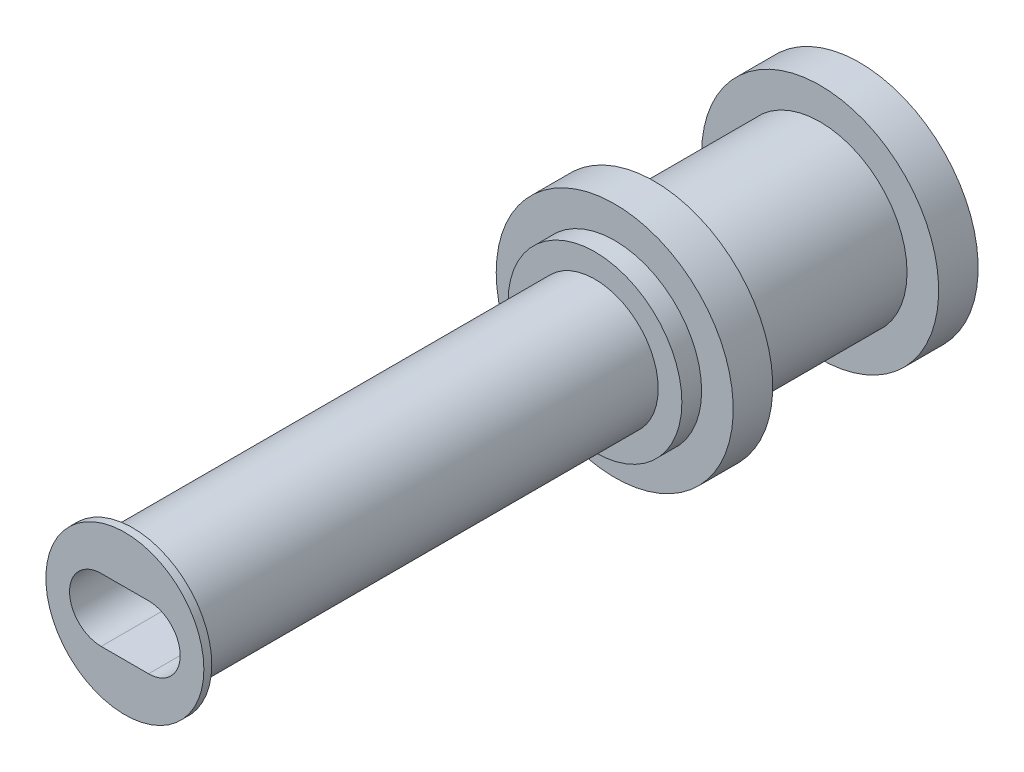
SolidWorks part; units mm, degrees
material "PVC Rigid"
ref_plane "Front Plane" through (0, 0, 0) normal (0, 0, 1) x (1, 0, 0)
ref_plane "Top Plane" through (0, 0, 0) normal (0, 1, 0) x (1, 0, 0)
ref_plane "Right Plane" through (0, 0, 0) normal (1, 0, 0) x (0, 0, -1)
sketch "Sketch1" plane through (0, 0, 0) normal (0, 0, 1) x (1, 0, 0)
  line L0 (-7.874, 0) -> (7.874, 0) construction
  line L1 (6.35, 0) -> (9.398, 0) construction
  line L2 (6.35, 0.762) -> (9.398, 0.762)
  line L10 (6.35, -0.762) -> (9.398, -0.762)
  line L19 (7.874, 1.524) -> (7.874, -1.524) construction
  line L20 (8.636, 1.524) -> (8.636, -1.524)
  line L21 (7.112, 1.524) -> (7.112, -1.524)
  line L22 (6.35, 0) -> (9.398, 0) construction
  circle A0 centre (7.874, 0) radius 2.794
  arc A2 (6.35, 0.762) -> (6.35, -0.762) centre (6.35, 0) ccw
  circle A4 centre (7.874, 0) radius 2.54
  arc A5 (9.398, -0.762) -> (9.398, 0.762) centre (9.398, 0) ccw
  circle A23 centre (7.874, 0) radius 2.286 construction
  arc A24 (8.636, 1.524) -> (7.112, 1.524) centre (7.874, 1.524) ccw
  arc A25 (7.112, -1.524) -> (8.636, -1.524) centre (7.874, -1.524) ccw
  point P13 (9.525, 0)
  point P14 (7.874, 0)
  point P15 (7.62, 0)
  point P17 (0, 3.302)
  point P18 (19.05, 3.302)
  point P19 (0, -3.302)
  point P20 (19.05, -3.302)
  point P23 (13.843, 0)
  point P24 (7.874, 0)
  point P25 (23.368, 0)
  point P26 (3.429, 0)
  point P27 (-7.874, -3.302)
  point P28 (7.874, -3.302)
  point P29 (-7.874, 3.302)
  point P30 (7.874, 3.302)
  point P35 (11.811, 0)
  point P60 (11.5175, 1.1139)
  point P70 (7.874, 0)
  point P77 (7.874, 0)
  dimension "D4" = 5.08
  dimension "D7" = 4.572
  dimension "D8" = 1.524
extrude "Boss-Extrude1" add sketch "Sketch1" along normal blind 3.937
sketch "Sketch2" plane through (0, 0, 0) normal (0, 0, -1) x (-1, 0, 0)
  circle A0 centre (-7.874, 0) radius 2.794
  circle A1 centre (-7.874, 0) radius 3.81
extrude "Boss-Extrude2" add sketch "Sketch2" against normal blind 1.27
ref_plane "Plane1" through (0, 0, 3.937) normal (0, 0, 1) x (1, 0, 0)
mirror "Mirror1" about plane through (0, 0, 3.937) normal (0, 0, 1) of "Boss-Extrude2", "Boss-Extrude1"
sketch "Sketch3" plane through (0, 0, 7.874) normal (0, 0, 1) x (1, 0, 0)
  circle A0 centre (7.874, 0) radius 2.794
extrude "Boss-Extrude3" add sketch "Sketch3" along normal blind 0.635
sketch "Sketch4" plane through (0, 0, 8.509) normal (0, 0, 1) x (1, 0, 0)
  circle A0 centre (7.874, 0) radius 2.032
extrude "Boss-Extrude4" add sketch "Sketch4" along normal blind 15.113
sketch "Sketch5" plane through (0, 0, 23.622) normal (0, 0, 1) x (1, 0, 0)
  circle A0 centre (7.874, 0) radius 2.032
  circle A1 centre (7.874, 0) radius 2.54
extrude "Boss-Extrude5" add sketch "Sketch5" against normal blind 0.254
sketch "Sketch6" plane through (0, 0, 23.622) normal (0, 0, 1) x (1, 0, 0)
  line L0 (8.636, 0) -> (7.112, 0) construction
  line L1 (8.636, -1.016) -> (7.112, -1.016)
  line L2 (8.636, 1.016) -> (7.112, 1.016)
  arc A0 (8.636, -1.016) -> (8.636, 1.016) centre (8.636, 0) ccw
  arc A1 (7.112, 1.016) -> (7.112, -1.016) centre (7.112, 0) ccw
  point P3 (7.874, 0)
extrude "Cut-Extrude1" cut sketch "Sketch6" along direction (0, 0, 1) on the side against the normal blind 15.24
